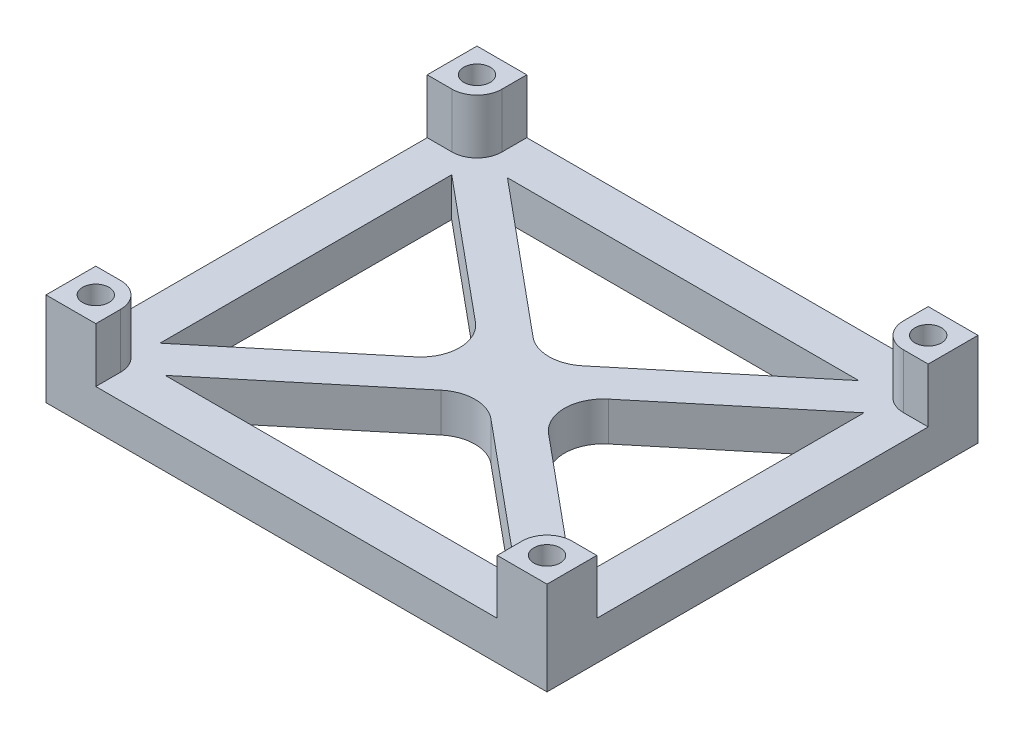
SolidWorks part; units mm, degrees
ref_plane "Front Plane" through (0, 0, 0) normal (0, 0, 1) x (1, 0, 0)
ref_plane "Top Plane" through (0, 0, 0) normal (0, 1, 0) x (1, 0, 0)
ref_plane "Right Plane" through (0, 0, 0) normal (1, 0, 0) x (0, 0, -1)
sketch "Sketch2" plane through (0, 0, 0) normal (0, 1, 0) x (1, 0, 0)
  line L0 (32.2, 27.7) -> (-32.2, 27.7)
  line L1 (29, -24.5) -> (-29, -24.5) construction
  line L2 (29, -24.5) -> (29, 24.5) construction
  line L3 (29, 24.5) -> (-29, 24.5) construction
  line L4 (-29, -24.5) -> (-29, 24.5) construction
  line L5 (29, -24.5) -> (-29, 24.5) construction
  line L6 (29, 24.5) -> (-29, -24.5) construction
  line L7 (-32.2, -27.7) -> (-32.2, 27.7)
  line L8 (32.2, -27.7) -> (-32.2, -27.7)
  line L9 (32.2, -27.7) -> (32.2, 27.7)
  line L11 (-26.5, -18.7508) -> (-26.5, 18.7508)
  line L13 (26.5, -18.7508) -> (26.5, 18.7508)
  line L14 (-26.5, 22) -> (26.5, -22) construction
  line L15 (-26.5, -22) -> (26.5, 22) construction
  line L16 (-26.5, 18.7508) -> (-3.9139, 0)
  line L17 (-22.5861, -22) -> (0, -3.2492)
  line L18 (-22.5861, 22) -> (0, 3.2492)
  line L19 (-26.5, -18.7508) -> (-3.9139, 0)
  line L20 (-28.0969, -20.0765) -> (24.9031, 23.9235) construction
  line L21 (-24.9031, -23.9235) -> (28.0969, 20.0765) construction
  line L22 (-26.5, -22) -> (-26.5, 22) construction
  line L23 (26.5, -22) -> (-26.5, -22) construction
  line L24 (-1.9569, -1.6246) -> (-1.9398, -1.6388)
  line L25 (-28.0969, 20.0765) -> (24.9031, -23.9235) construction
  line L26 (-1.9569, 1.6246) -> (-1.9398, 1.6388)
  line L27 (0, 3.2492) -> (22.5861, 22)
  line L28 (1.9398, 1.6388) -> (1.9569, 1.6246)
  line L29 (-24.9031, 23.9235) -> (28.0969, -20.0765) construction
  line L30 (3.9139, 0) -> (26.5, -18.7508)
  line L31 (3.9139, 0) -> (26.5, 18.7508)
  line L32 (1.9398, -1.6388) -> (1.9569, -1.6246)
  line L33 (0, -3.2492) -> (22.5861, -22)
  line L34 (22.5861, -22) -> (-22.5861, -22)
  line L35 (26.5, -22) -> (26.5, 22) construction
  line L36 (22.5861, 22) -> (-22.5861, 22)
  line L37 (26.5, 22) -> (-26.5, 22) construction
  circle A0 centre (-29, 24.5) radius 1.7
  circle A1 centre (29, 24.5) radius 1.7
  circle A2 centre (29, -24.5) radius 1.7
  circle A3 centre (-29, -24.5) radius 1.7
  point P0 (0, 0)
  dimension "D7" = 3.4
  dimension "D1" = 58
  dimension "D2" = 49
  dimension "2.5" = 2.5
  dimension "D8" = 2.5
  dimension "D3" = 3.2
  dimension "D4" = 2.5
  dimension "D5" = 2.5
  dimension "D6" = 2.5
extrude "Boss-Extrude1" add sketch "Sketch2" along normal blind 5
fillet "Fillet1" radius 5 4 edges at (0, 2.5, 3.2492) (3.9139, 2.5, 0) (0, 2.5, -3.2492) (-3.9139, 2.5, 0)
sketch "Sketch3" plane through (0, 5, 0) normal (0, 1, 0) x (1, 0, 0)
  line L2 (-32.2, -27.7) -> (-32.2, 27.7) construction
  line L3 (-32.2, -21.3) -> (-32.2, -27.7)
  line L4 (-32.2, -27.7) -> (-29, -27.7)
  line L5 (-29, -21.3) -> (-32.2, -21.3)
  line L6 (-25.8, -24.5) -> (-25.8, -27.7)
  line L7 (32.2, -27.7) -> (-32.2, -27.7) construction
  line L8 (-25.8, -27.7) -> (-32.2, -27.7)
  line L9 (-29, 21.3) -> (-32.2, 21.3)
  line L10 (-32.2, 21.3) -> (-32.2, 27.7)
  line L11 (-32.2, 27.7) -> (-25.8, 27.7)
  line L12 (32.2, 27.7) -> (-32.2, 27.7) construction
  line L13 (-25.8, 27.7) -> (-25.8, 24.5)
  line L14 (25.8, 24.5) -> (25.8, 27.7)
  line L15 (25.8, 27.7) -> (32.2, 27.7)
  line L16 (32.2, 27.7) -> (32.2, 21.3)
  line L17 (32.2, -27.7) -> (32.2, 27.7) construction
  line L18 (32.2, 21.3) -> (29, 21.3)
  line L19 (25.8, -24.5) -> (25.8, -27.7)
  line L20 (25.8, -27.7) -> (32.2, -27.7)
  line L21 (32.2, -27.7) -> (32.2, -21.3)
  line L22 (32.2, -21.3) -> (29, -21.3)
  circle A1 centre (-29, 24.5) radius 1.7
  circle A2 centre (-29, 24.5) radius 1.7 construction
  circle A3 centre (29, 24.5) radius 1.7
  circle A4 centre (29, -24.5) radius 1.7
  circle A5 centre (-29, -24.5) radius 1.7
  arc A6 (-25.8, -24.5) -> (-29, -21.3) centre (-29, -24.5) ccw
  arc A7 (29, -21.3) -> (25.8, -24.5) centre (29, -24.5) ccw
  arc A8 (25.8, 24.5) -> (29, 21.3) centre (29, 24.5) ccw
  arc A9 (-29, 21.3) -> (-25.8, 24.5) centre (-29, 24.5) ccw
  circle M2 centre (-29, -24.5) radius 1.7
  circle M3 centre (29, -24.5) radius 1.7
  circle M4 centre (29, 24.5) radius 1.7
  circle M5 centre (-29, 24.5) radius 1.7
  line M14 (-32.2, -27.7) -> (32.2, -27.7)
  line M15 (32.2, -27.7) -> (32.2, 27.7)
  line M16 (32.2, 27.7) -> (-32.2, 27.7)
  line M17 (-32.2, 27.7) -> (-32.2, -27.7)
extrude "Boss-Extrude2" add sketch "Sketch3" along normal blind 7 contours L6 A6 L5 M17 M14 M2 | L9 A9 L13 M16 M17 M5 | L14 A8 L18 M15 M16 M4 | L22 A7 L19 M14 M15 M3 | A5
